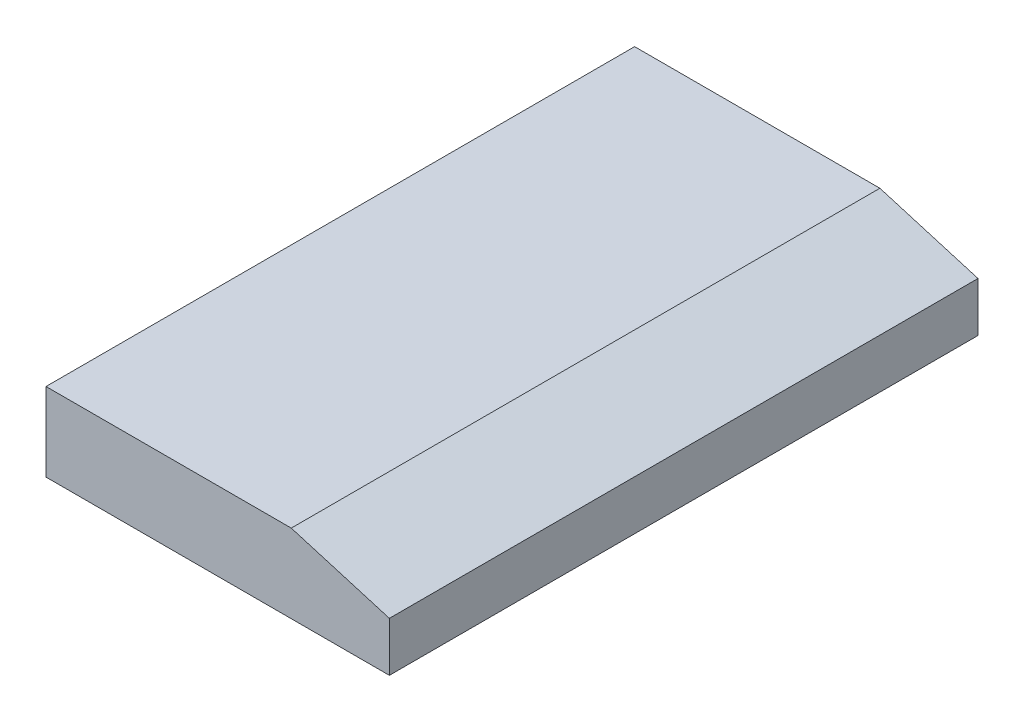
SolidWorks part; units mm, degrees
ref_plane "Alzado" through (0, 0, 0) normal (0, 0, 1) x (1, 0, 0)
ref_plane "Planta" through (0, 0, 0) normal (0, 1, 0) x (1, 0, 0)
ref_plane "Vista lateral" through (0, 0, 0) normal (1, 0, 0) x (0, 0, -1)
sketch "Croquis1" plane through (0, 0, 0) normal (0, 0, 1) x (1, 0, 0)
  line L1 (-175, -40) -> (175, -40)
  line L2 (-175, -40) -> (-175, 40)
  line L3 (-175, 40) -> (75, 40)
  line L4 (175, -40) -> (175, 10.3484)
  line L7 (75, 40) -> (175, 10.3484)
  point P0 (0, 0)
extrude "Saliente-Extruir1" add sketch "Croquis1" along normal blind 600 contours L3 L7 L4 L1 L2
